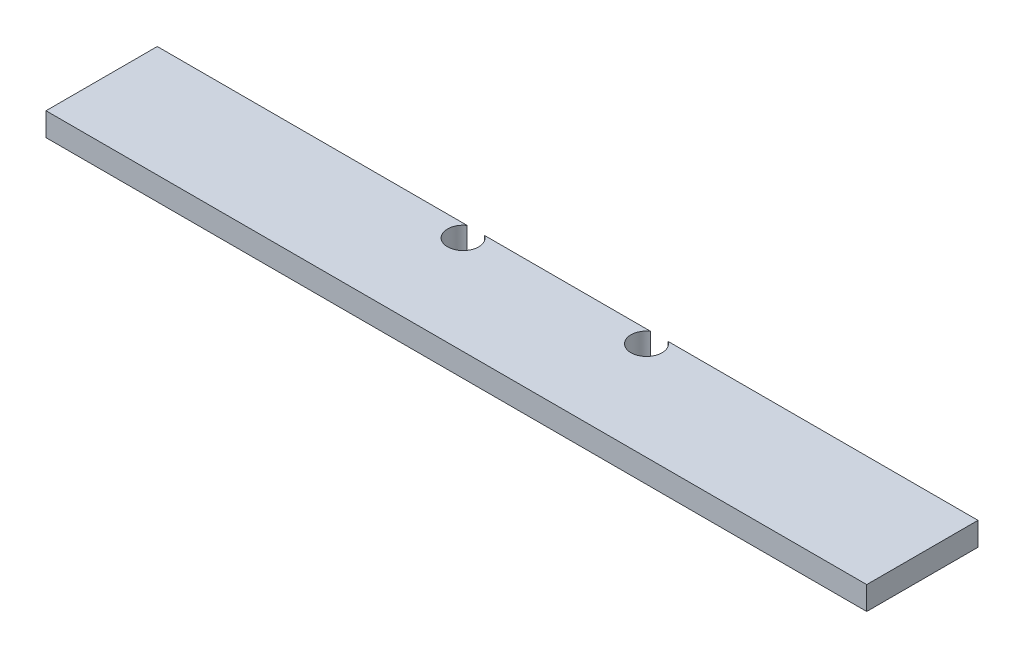
SolidWorks part; units mm, degrees
material "Oak"
ref_plane "Front Plane" through (0, 0, 0) normal (0, 0, 1) x (1, 0, 0)
ref_plane "Top Plane" through (0, 0, 0) normal (0, 1, 0) x (1, 0, 0)
ref_plane "Right Plane" through (0, 0, 0) normal (1, 0, 0) x (0, 0, -1)
sketch "Sketch1" plane through (0, 0, 0) normal (0, 1, 0) x (1, 0, 0)
  line L1 (0, 0) -> (669.925, 0)
  line L2 (0, 0) -> (0, 90.8304)
  line L3 (0, 90.8304) -> (669.925, 90.8304)
  line L4 (669.925, 0) -> (669.925, 90.8304)
  dimension "D1" = 90.8304
  dimension "D2" = 669.925
extrude "Boss-Extrude1" add sketch "Sketch1" along normal blind 19.05
sketch "Sketch2" plane through (0, 0, 0) normal (0, -1, 0) x (1, 0, 0)
  line L0 (260.1214, -80.3402) -> (409.8036, -80.3402) construction
  line L1 (669.925, 0) -> (669.925, -90.8304) construction
  line L3 (0, -90.8304) -> (0, 0) construction
  line L6 (669.925, -90.8304) -> (0, -90.8304) construction
  circle A0 centre (409.8036, -80.3402) radius 12.7
  circle A1 centre (260.1214, -80.3402) radius 12.7
  dimension "D1" = 25.4
  dimension "D2" = 409.8036
  dimension "D4" = 409.8036
  dimension "D3" = 10.4902
extrude "Cut-Extrude4" cut sketch "Sketch2" against normal through all
